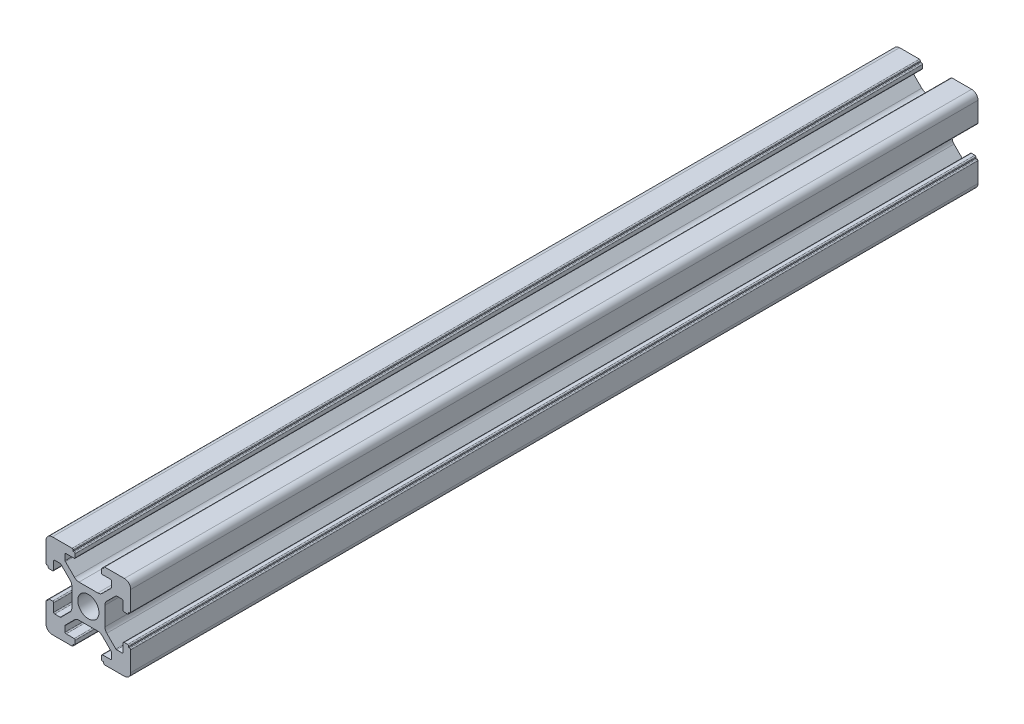
SolidWorks part; units mm, degrees
material "1060 Alloy"
ref_plane "前视基准面" through (0, 0, 0) normal (0, 0, 1) x (1, 0, 0)
ref_plane "上视基准面" through (0, 0, 0) normal (0, 1, 0) x (1, 0, 0)
ref_plane "右视基准面" through (0, 0, 0) normal (1, 0, 0) x (0, 0, -1)
sketch "草图1" plane through (0, 0, 0) normal (0, 0, 1) x (1, 0, 0)
  line L0 (0, 0) -> (0, 5.5) construction
  line L1 (-8.5023, -10.0023) -> (-3.85, -10.0023)
  line L2 (-10.0023, -8.5023) -> (-10.0023, -3.85)
  line L3 (-8.5023, 10.0023) -> (-3.85, 10.0023)
  line L4 (10.0023, -8.5023) -> (10.0023, -3.85)
  line L5 (-10.0023, -10.0023) -> (10.0023, 10.0023) construction
  line L6 (-10.0023, 10.0023) -> (10.0023, -10.0023) construction
  line L7 (-2.218, -3.9) -> (2.218, -3.9)
  line L8 (-3.9, -2.218) -> (-3.9, 2.218)
  line L9 (-2.218, 3.9) -> (2.218, 3.9)
  line L10 (3.9, -2.218) -> (3.9, 2.218)
  line L11 (-3.9, -3.9) -> (3.9, 3.9) construction
  line L12 (-3.9, 3.9) -> (3.9, -3.9) construction
  line L13 (-5.25, -8.2) -> (-3.35, -8.2)
  line L14 (-8.2, -5.25) -> (-8.2, -3.35)
  line L15 (-5.25, 8.2) -> (-3.35, 8.2)
  line L16 (8.2, -5.25) -> (8.2, -3.35)
  line L17 (-8.2, -8.2) -> (8.2, 8.2) construction
  line L18 (-8.2, 8.2) -> (8.2, -8.2) construction
  line L19 (-7.95, 5.5) -> (-6.6642, 5.5)
  line L20 (0, 0) -> (5.5, 0) construction
  line L23 (-5.5, 7.95) -> (-5.5, 6.6642)
  line L26 (0, 0) -> (-0.5303, 0.5303)
  line L27 (3.2787, 4.3393) -> (5.4268, 6.4874)
  line L28 (0, 0) -> (0.5303, -0.5303)
  line L29 (5.5, 6.6642) -> (5.5, 7.95)
  line L30 (4.3393, 3.2787) -> (6.4874, 5.4268)
  line L31 (6.6642, 5.5) -> (7.95, 5.5)
  line L32 (4.3393, -3.2787) -> (6.4874, -5.4268)
  line L33 (3.2787, -4.3393) -> (5.4268, -6.4874)
  line L34 (-3.2787, -4.3393) -> (-5.4268, -6.4874)
  line L35 (-4.3393, -3.2787) -> (-6.4874, -5.4268)
  line L36 (-4.3393, 3.2787) -> (-6.4874, 5.4268)
  line L37 (-3.2787, 4.3393) -> (-5.4268, 6.4874)
  line L38 (3.1, -8.45) -> (3.1, -9.2523)
  line L39 (8.45, 3.1) -> (9.2523, 3.1)
  line L40 (-5.5, -6.6642) -> (-5.5, -7.95)
  line L41 (-6.6642, -5.5) -> (-7.95, -5.5)
  line L42 (5.5, -6.6642) -> (5.5, -7.95)
  line L43 (6.6642, -5.5) -> (7.95, -5.5)
  line L44 (9.2523, -3.1) -> (8.45, -3.1)
  line L46 (10.0023, 3.85) -> (10.0023, 8.5023)
  line L47 (8.2, 3.35) -> (8.2, 5.25)
  line L48 (-3.1, -9.2523) -> (-3.1, -8.45)
  line L49 (-8.45, -3.1) -> (-9.2523, -3.1)
  line L50 (-9.2523, 3.1) -> (-8.45, 3.1)
  line L51 (-3.1, 8.45) -> (-3.1, 9.2523)
  line L52 (3.1, 9.2523) -> (3.1, 8.45)
  line L53 (3.85, 10.0023) -> (8.5023, 10.0023)
  line L54 (3.35, 8.2) -> (5.25, 8.2)
  line L55 (-10.0023, 3.85) -> (-10.0023, 8.5023)
  line L56 (-8.2, 3.35) -> (-8.2, 5.25)
  line L57 (3.35, -8.2) -> (5.25, -8.2)
  line L58 (3.85, -10.0023) -> (8.5023, -10.0023)
  line L59 (9.7523, -3.6) -> (9.5023, -3.6)
  line L61 (9.7523, 3.6) -> (9.5023, 3.6)
  line L62 (9.5023, -3.6) -> (9.5023, -3.35)
  line L63 (3.6, -9.7523) -> (3.6, -9.5023)
  line L64 (3.35, -9.5023) -> (3.6, -9.5023)
  line L65 (9.5023, 3.35) -> (9.5023, 3.6)
  line L66 (-3.6, -9.5023) -> (-3.35, -9.5023)
  line L67 (-3.6, -9.7523) -> (-3.6, -9.5023)
  line L68 (-9.7523, -3.6) -> (-9.5023, -3.6)
  line L69 (-9.5023, -3.35) -> (-9.5023, -3.6)
  line L70 (-9.5023, 3.6) -> (-9.5023, 3.35)
  line L71 (-9.7523, 3.6) -> (-9.5023, 3.6)
  line L72 (-3.6, 9.7523) -> (-3.6, 9.5023)
  line L73 (-3.35, 9.5023) -> (-3.6, 9.5023)
  line L74 (3.6, 9.5023) -> (3.35, 9.5023)
  line L75 (3.6, 9.7523) -> (3.6, 9.5023)
  circle A0 centre (0, 0) radius 2.5
  arc A1 (10.0023, 8.5023) -> (8.5023, 10.0023) centre (8.5023, 8.5023) ccw
  arc A2 (8.5023, -10.0023) -> (10.0023, -8.5023) centre (8.5023, -8.5023) ccw
  arc A3 (-10.0023, -8.5023) -> (-8.5023, -10.0023) centre (-8.5023, -8.5023) ccw
  arc A4 (-10.0023, 8.5023) -> (-8.5023, 10.0023) centre (-8.5023, 8.5023) cw
  arc A5 (-9.5023, -3.35) -> (-9.2523, -3.1) centre (-9.2523, -3.35) cw
  arc A6 (-9.7523, -3.6) -> (-10.0023, -3.85) centre (-9.7523, -3.85) ccw
  arc A7 (-8.45, -3.1) -> (-8.2, -3.35) centre (-8.45, -3.35) cw
  arc A8 (-7.95, -5.5) -> (-8.2, -5.25) centre (-7.95, -5.25) cw
  arc A9 (-6.4874, -5.4268) -> (-6.6642, -5.5) centre (-6.6642, -5.25) cw
  arc A10 (-5.4268, -6.4874) -> (-5.5, -6.6642) centre (-5.25, -6.6642) ccw
  arc A11 (-5.5, -7.95) -> (-5.25, -8.2) centre (-5.25, -7.95) ccw
  arc A12 (-3.6, -9.7523) -> (-3.85, -10.0023) centre (-3.85, -9.7523) cw
  arc A13 (-3.35, -9.5023) -> (-3.1, -9.2523) centre (-3.35, -9.2523) ccw
  arc A14 (-3.1, -8.45) -> (-3.35, -8.2) centre (-3.35, -8.45) ccw
  arc A15 (3.1, -8.45) -> (3.35, -8.2) centre (3.35, -8.45) cw
  arc A16 (5.5, -7.95) -> (5.25, -8.2) centre (5.25, -7.95) cw
  arc A17 (5.4268, -6.4874) -> (5.5, -6.6642) centre (5.25, -6.6642) cw
  arc A18 (6.4874, -5.4268) -> (6.6642, -5.5) centre (6.6642, -5.25) ccw
  arc A19 (7.95, -5.5) -> (8.2, -5.25) centre (7.95, -5.25) ccw
  arc A20 (8.45, -3.1) -> (8.2, -3.35) centre (8.45, -3.35) ccw
  arc A21 (9.5023, -3.35) -> (9.2523, -3.1) centre (9.2523, -3.35) ccw
  arc A22 (9.7523, -3.6) -> (10.0023, -3.85) centre (9.7523, -3.85) cw
  arc A23 (3.35, -9.5023) -> (3.1, -9.2523) centre (3.35, -9.2523) cw
  arc A24 (3.6, -9.7523) -> (3.85, -10.0023) centre (3.85, -9.7523) ccw
  arc A25 (7.95, 5.5) -> (8.2, 5.25) centre (7.95, 5.25) cw
  arc A26 (8.2, 3.35) -> (8.45, 3.1) centre (8.45, 3.35) ccw
  arc A27 (9.5023, 3.35) -> (9.2523, 3.1) centre (9.2523, 3.35) cw
  arc A28 (9.7523, 3.6) -> (10.0023, 3.85) centre (9.7523, 3.85) ccw
  arc A29 (6.6642, 5.5) -> (6.4874, 5.4268) centre (6.6642, 5.25) ccw
  arc A30 (5.4268, 6.4874) -> (5.5, 6.6642) centre (5.25, 6.6642) ccw
  arc A31 (5.5, 7.95) -> (5.25, 8.2) centre (5.25, 7.95) ccw
  arc A32 (3.1, 8.45) -> (3.35, 8.2) centre (3.35, 8.45) ccw
  arc A33 (3.6, 9.7523) -> (3.85, 10.0023) centre (3.85, 9.7523) cw
  arc A34 (3.35, 9.5023) -> (3.1, 9.2523) centre (3.35, 9.2523) ccw
  arc A35 (-9.7523, 3.6) -> (-10.0023, 3.85) centre (-9.7523, 3.85) cw
  arc A36 (-9.5023, 3.35) -> (-9.2523, 3.1) centre (-9.2523, 3.35) ccw
  arc A37 (-8.45, 3.1) -> (-8.2, 3.35) centre (-8.45, 3.35) ccw
  arc A38 (-8.2, 5.25) -> (-7.95, 5.5) centre (-7.95, 5.25) cw
  arc A39 (-6.4874, 5.4268) -> (-6.6642, 5.5) centre (-6.6642, 5.25) ccw
  arc A40 (-5.4268, 6.4874) -> (-5.5, 6.6642) centre (-5.25, 6.6642) cw
  arc A41 (-5.5, 7.95) -> (-5.25, 8.2) centre (-5.25, 7.95) cw
  arc A42 (-3.1, 8.45) -> (-3.35, 8.2) centre (-3.35, 8.45) cw
  arc A43 (-3.1, 9.2523) -> (-3.35, 9.5023) centre (-3.35, 9.2523) ccw
  arc A44 (-3.6, 9.7523) -> (-3.85, 10.0023) centre (-3.85, 9.7523) ccw
  arc A45 (-4.3393, 3.2787) -> (-3.9, 2.218) centre (-5.4, 2.218) cw
  arc A46 (-3.2787, 4.3393) -> (-2.218, 3.9) centre (-2.218, 5.4) ccw
  arc A47 (3.2787, 4.3393) -> (2.218, 3.9) centre (2.218, 5.4) cw
  arc A48 (4.3393, 3.2787) -> (3.9, 2.218) centre (5.4, 2.218) ccw
  arc A49 (4.3393, -3.2787) -> (3.9, -2.218) centre (5.4, -2.218) cw
  arc A50 (3.2787, -4.3393) -> (2.218, -3.9) centre (2.218, -5.4) ccw
  arc A51 (-4.3393, -3.2787) -> (-3.9, -2.218) centre (-5.4, -2.218) ccw
  arc A52 (-2.218, -3.9) -> (-3.2787, -4.3393) centre (-2.218, -5.4) ccw
  point P0 (0, 0)
  point P7 (10.0023, 0)
  point P62 (0, 0)
  point P76 (0, 0)
  point P92 (-8.2, -5.5)
  point P99 (0, 0)
  point P106 (-5.5, -8.2)
  point P117 (5.5, -8.2)
  point P124 (8.2, -5.5)
  point P137 (8.2, 5.5)
  point P140 (8.2, 3.1)
  point P147 (6.5607, 5.5)
  point P152 (5.5, 8.2)
  point P167 (-8.2, 5.5)
  point P174 (-5.5, 8.2)
  dimension "D1" = 1.5
  dimension "D5" = 0.25
  dimension "D6" = 1.5
  dimension "D2" = 4
  dimension "D3" = 4
  dimension "D4" = 4
extrude "凸台-拉伸1" add sketch "草图1" along normal blind 200 contours A52 L7 A50 L33 A17 L42 A16 L57 A15 L38 A23 L64 L63 A24 L58 A2 L4 A22 L59 L62 A21 L44 A20 L16 A19 L43 A18 L32 A49 L10 A48 L30 A29 L31 A25 L47 A26 L39 A27 L65 L61 A28 L46 A1 L53 A33 L75 L74 A34 L52 A32
ref_plane "Plane1" through (0, 0, 100) normal (0, 0, 1) x (1, 0, 0)
